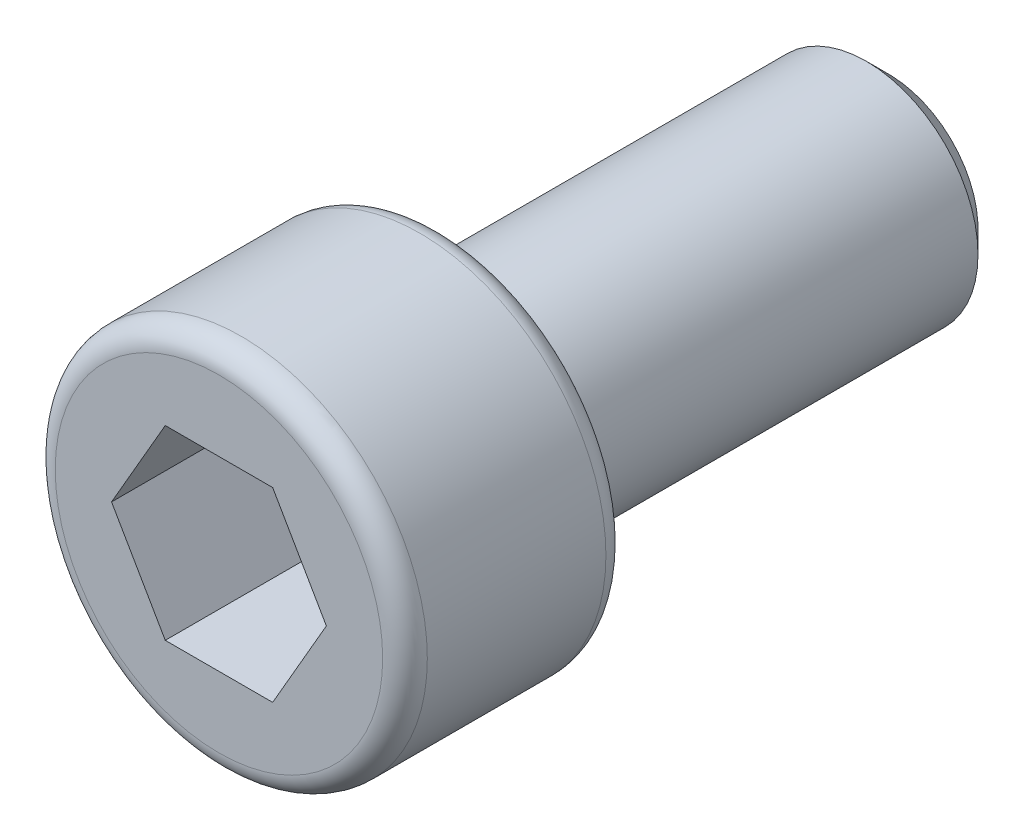
SolidWorks part; units mm, degrees
ref_plane "前视基准面" through (0, 0, 0) normal (0, 0, 1) x (1, 0, 0)
ref_plane "上视基准面" through (0, 0, 0) normal (0, 1, 0) x (1, 0, 0)
ref_plane "右视基准面" through (0, 0, 0) normal (1, 0, 0) x (0, 0, -1)
sketch "草图1" plane through (0, 0, 0) normal (0, 0, 1) x (1, 0, 0)
  circle A0 centre (0, 0) radius 2.5
  dimension "D1" = 5
extrude "凸台-拉伸1" add sketch "草图1" along normal blind 3
sketch "草图2" plane through (0, 0, 0) normal (0, 0, -1) x (-1, 0, 0)
  circle A0 centre (0, 0) radius 1.5
  dimension "D1" = 3
extrude "凸台-拉伸2" add sketch "草图2" along normal blind 6
sketch "草图3" plane through (0, 0, 3) normal (0, 0, 1) x (1, 0, 0)
  line L1 (1.4434, 0) -> (0.7217, 1.25)
  line L2 (0.7217, 1.25) -> (-0.7217, 1.25)
  line L3 (-0.7217, 1.25) -> (-1.4434, 0)
  line L4 (-1.4434, 0) -> (-0.7217, -1.25)
  line L5 (-0.7217, -1.25) -> (0.7217, -1.25)
  line L6 (0.7217, -1.25) -> (1.4434, 0)
  circle A0 centre (0, 0) radius 1.25 construction
  dimension "D1" = 2.5
extrude "切除-拉伸1" cut sketch "草图3" against normal blind 2
chamfer "倒角1" distance 0.3 angle 45 1 edges at (-1.5, 0, -6)
fillet "圆角1" radius 0.3 2 edges at (2.5, 0, 0) (2.5, 0, 3)
